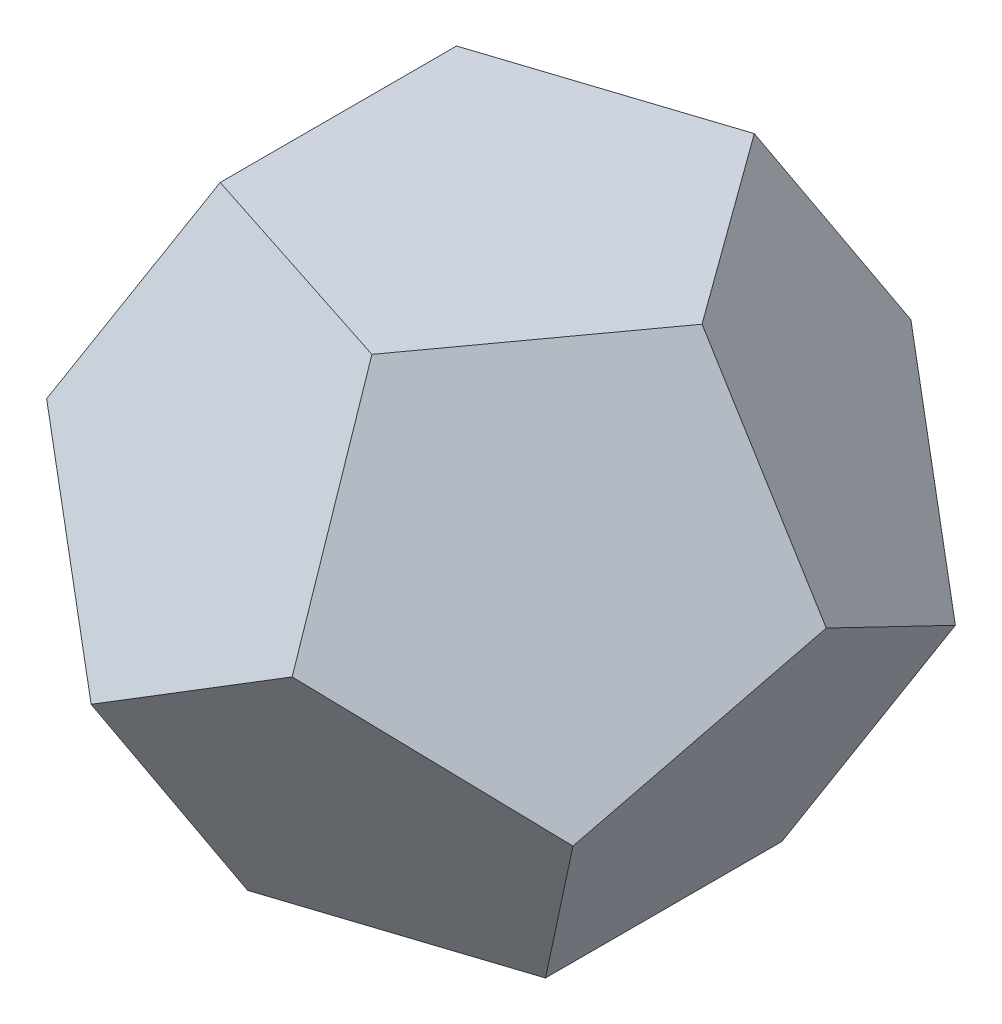
SolidWorks part; units mm, degrees
ref_plane "Vorderansicht-XY" through (0, 0, 0) normal (0, 0, 1) x (1, 0, 0)
ref_plane "Draufsicht-ZX" through (0, 0, 0) normal (0, 1, 0) x (1, 0, 0)
ref_plane "Seitenansicht-YZ" through (0, 0, 0) normal (1, 0, 0) x (0, 0, -1)
sketch "Skizze1" plane through (0, 0, 0) normal (0, 1, 0) x (1, 0, 0)
  line L0 (-37.8505, 0) -> (37.8505, 0) construction
  line L1 (42.5325, 0) -> (13.1433, 40.4508)
  line L2 (13.1433, 40.4508) -> (-34.4095, 25)
  line L3 (-34.4095, 25) -> (-34.4095, -25)
  line L4 (-34.4095, -25) -> (13.1433, -40.4508)
  line L5 (13.1433, -40.4508) -> (42.5325, 0)
  circle A0 centre (0, 0) radius 34.4095 construction
  dimension "D1" = 50
sketch3d "3D-Skizze1"
  line L0 (13.1433, 0, 40.4508) -> (21.2663, -42.5325, 65.4508)
  line L1 (13.1433, 0, -40.4508) -> (21.2663, -42.5325, -65.4508)
  line L2 (21.2663, -42.5325, -65.4508) -> (-21.2663, -68.8191, -65.4508)
  line L3 (-21.2663, -68.8191, -65.4508) -> (-55.6758, -42.5325, -40.4508)
  line L4 (13.1433, 0, 40.4508) -> (42.5325, 0, 0) construction
  line L5 (-34.4095, 0, 25) -> (-55.6758, -42.5325, 40.4508)
  line L6 (-55.6758, -42.5325, 40.4508) -> (-21.2663, -68.8191, 65.4508)
  line L7 (-21.2663, -68.8191, 65.4508) -> (21.2663, -42.5325, 65.4508)
  line L8 (-34.4095, 0, 25) -> (13.1433, 0, 40.4508) construction
  line L9 (-34.4095, 0, -25) -> (-55.6758, -42.5325, -40.4508)
  line L10 (-55.6758, -42.5325, -40.4508) -> (-68.8191, -68.8191, 0)
  line L11 (-68.8191, -68.8191, 0) -> (-55.6758, -42.5325, 40.4508)
  line L12 (-34.4095, 0, -25) -> (-34.4095, 0, 25) construction
  line L13 (13.1433, 0, -40.4508) -> (-34.4095, 0, -25) construction
  line L14 (-21.2663, -68.8191, -65.4508) -> (-10.6331, 0, -32.7254) construction
  line L15 (21.2663, -42.5325, -65.4508) -> (-45.0427, -21.2663, -32.7254) construction
  line L16 (-21.2663, -68.8191, 65.4508) -> (-10.6331, 0, 32.7254) construction
  line L18 (-55.6758, -42.5325, -40.4508) -> (17.2048, -21.2663, -52.9508) construction
  line L31 (-55.6758, -42.5325, 40.4508) -> (17.2048, -21.2663, 52.9508) construction
  line L32 (21.2663, -42.5325, 65.4508) -> (-45.0427, -21.2663, 32.7254) construction
  line L33 (-55.6758, -42.5325, -40.4508) -> (-45.0427, -21.2663, 32.7254) construction
  line L34 (-68.8191, -68.8191, 0) -> (-34.4095, 0, 0) construction
  line L35 (-55.6758, -42.5325, 40.4508) -> (-45.0427, -21.2663, -32.7254) construction
  point P5 (-15.3884, -30.7768, -47.3607)
  point P41 (-49.798, -30.7768, 0)
  point P43 (-15.3884, -30.7768, 47.3607)
sketch3d "3D-Skizze2"
  line L0 (42.5325, 0, 0) -> (68.8191, -42.5325, 0)
  line L1 (68.8191, -42.5325, 0) -> (55.6758, -68.8191, 40.4508)
  line L2 (55.6758, -68.8191, 40.4508) -> (21.2663, -42.5325, 65.4508)
  line L3 (13.1433, 0, 40.4508) -> (42.5325, 0, 0) construction
  line L4 (55.6758, -68.8191, 40.4508) -> (27.8379, 0, 20.2254) construction
  line L5 (21.2663, -42.5325, 65.4508) -> (55.6758, -21.2663, 0) construction
  line L6 (68.8191, -42.5325, 0) -> (17.2048, -21.2663, 52.9508) construction
  line L7 (68.8191, -42.5325, 0) -> (55.6758, -68.8191, -40.4508)
  line L8 (55.6758, -68.8191, -40.4508) -> (21.2663, -42.5325, -65.4508)
  line L9 (42.5325, 0, 0) -> (13.1433, 0, -40.4508) construction
  line L10 (55.6758, -68.8191, -40.4508) -> (27.8379, 0, -20.2254) construction
  line L11 (68.8191, -42.5325, 0) -> (17.2048, -21.2663, -52.9508) construction
  line L12 (21.2663, -42.5325, -65.4508) -> (55.6758, -21.2663, 0) construction
  line L13 (55.6758, -68.8191, 40.4508) -> (34.4095, -111.3516, 25)
  line L14 (34.4095, -111.3516, 25) -> (34.4095, -111.3516, -25)
  line L15 (34.4095, -111.3516, -25) -> (55.6758, -68.8191, -40.4508)
  line L16 (68.8191, -42.5325, 0) -> (34.4095, -111.3516, 0) construction
  line L17 (55.6758, -68.8191, 40.4508) -> (45.0427, -90.0854, -32.7254) construction
  line L18 (55.6758, -68.8191, -40.4508) -> (45.0427, -90.0854, 32.7254) construction
  line L19 (-21.2663, -68.8191, -65.4508) -> (-13.1433, -111.3516, -40.4508)
  line L20 (-13.1433, -111.3516, -40.4508) -> (34.4095, -111.3516, -25)
  line L21 (55.6758, -68.8191, -40.4508) -> (-17.2048, -90.0854, -52.9508) construction
  line L22 (21.2663, -42.5325, -65.4508) -> (10.6331, -111.3516, -32.7254) construction
  line L23 (-21.2663, -68.8191, -65.4508) -> (45.0427, -90.0854, -32.7254) construction
  line L24 (-21.2663, -68.8191, 65.4508) -> (-13.1433, -111.3516, 40.4508)
  line L25 (-13.1433, -111.3516, 40.4508) -> (34.4095, -111.3516, 25)
  line L26 (-13.1433, -111.3516, 40.4508) -> (38.471, -55.6758, 52.9508) construction
  line L27 (-21.2663, -68.8191, 65.4508) -> (45.0427, -90.0854, 32.7254) construction
  line L28 (-68.8191, -68.8191, 0) -> (-42.5325, -111.3516, 0)
  line L29 (-42.5325, -111.3516, 0) -> (-13.1433, -111.3516, 40.4508)
  line L30 (-34.4095, 0, 25) -> (13.1433, 0, 40.4508) construction
  line L31 (-55.6758, -42.5325, 40.4508) -> (-27.8379, -111.3516, 20.2254) construction
  line L32 (-68.8191, -68.8191, 0) -> (-17.2048, -90.0854, 52.9508) construction
  line L33 (-13.1433, -111.3516, -40.4508) -> (-42.5325, -111.3516, 0)
  point P10 (40.2874, -30.7768, 29.2705)
  point P21 (40.2874, -30.7768, -29.2705)
  point P25 (49.798, -80.5748, 0)
  point P33 (15.3884, -80.5748, -47.3607)
  point P34 (15.3884, -80.5748, 47.3607)
  point P48 (-40.2874, -80.5748, 29.2705)
surface "Oberfläche-Ebene1" sketch "Skizze1"
ref_plane "Ebene2" through (22.2703, 13.7638, -16.1803) normal (-0.7236, -0.4472, 0.5257) x (0.4472, 0.2764, 0.8507)
sketch "Skizze2" plane through (22.2703, 13.7638, -16.1803) normal (-0.7236, -0.4472, 0.5257) x (0.4472, 0.2764, 0.8507)
  line L0 (19.0211, -22.3607) -> (-28.5317, -6.9098) construction
  line L1 (19.0211, -22.3607) -> (-28.5317, -6.9098)
  line L2 (19.0211, -22.3607) -> (19.0211, -72.3607) construction
  line L3 (19.0211, -22.3607) -> (19.0211, -72.3607)
  line L4 (19.0211, -72.3607) -> (-28.5317, -87.8115) construction
  line L5 (19.0211, -72.3607) -> (-28.5317, -87.8115)
  line L6 (-28.5317, -87.8115) -> (-57.921, -47.3607) construction
  line L7 (-28.5317, -87.8115) -> (-57.921, -47.3607)
  line L8 (-28.5317, -6.9098) -> (-57.921, -47.3607) construction
  line L9 (-28.5317, -6.9098) -> (-57.921, -47.3607)
surface "Oberfläche-Ebene2" sketch "Skizze2"
ref_plane "Ebene3" through (22.2703, 13.7638, 16.1803) normal (-0.7236, -0.4472, -0.5257) x (-0.4472, -0.2764, 0.8507)
sketch "Skizze3" plane through (22.2703, 13.7638, 16.1803) normal (-0.7236, -0.4472, -0.5257) x (-0.4472, -0.2764, 0.8507)
  line L0 (-19.0211, -22.3607) -> (-19.0211, -72.3607) construction
  line L1 (-19.0211, -72.3607) -> (28.5317, -87.8115) construction
  line L2 (28.5317, -87.8115) -> (57.921, -47.3607) construction
  line L3 (28.5317, -6.9098) -> (57.921, -47.3607) construction
  line L4 (28.5317, -6.9098) -> (-19.0211, -22.3607) construction
  line L5 (-19.0211, -22.3607) -> (-19.0211, -72.3607)
  line L6 (-19.0211, -72.3607) -> (28.5317, -87.8115)
  line L7 (28.5317, -87.8115) -> (57.921, -47.3607)
  line L8 (28.5317, -6.9098) -> (57.921, -47.3607)
  line L9 (28.5317, -6.9098) -> (-19.0211, -22.3607)
surface "Oberfläche-Ebene3" sketch "Skizze3"
ref_plane "Ebene4" through (-8.5065, 13.7638, 26.1803) normal (0.2764, -0.4472, -0.8507) x (-0.961, -0.1286, -0.2446)
sketch "Skizze4" plane through (-8.5065, 13.7638, 26.1803) normal (0.2764, -0.4472, -0.8507) x (-0.961, -0.1286, -0.2446)
  line L0 (13.277, -91.3709) -> (-30.9796, -68.1039) construction
  line L1 (49.0813, -56.4703) -> (13.277, -91.3709) construction
  line L2 (-22.5273, -18.8234) -> (-30.9796, -68.1039) construction
  line L3 (26.953, -11.6335) -> (49.0813, -56.4703) construction
  line L4 (26.953, -11.6335) -> (-22.5273, -18.8234) construction
  line L5 (13.277, -91.3709) -> (-30.9796, -68.1039)
  line L6 (49.0813, -56.4703) -> (13.277, -91.3709)
  line L7 (-22.5273, -18.8234) -> (-30.9796, -68.1039)
  line L8 (26.953, -11.6335) -> (49.0813, -56.4703)
  line L9 (26.953, -11.6335) -> (-22.5273, -18.8234)
surface "Oberfläche-Ebene4" sketch "Skizze4"
ref_plane "Ebene5" through (-27.5276, 13.7638, 0) normal (0.8944, -0.4472, 0) x (0, 0, -1)
sketch "Skizze5" plane through (-27.5276, 13.7638, 0) normal (0.8944, -0.4472, 0) x (0, 0, -1)
  line L0 (40.4508, -62.9412) -> (0, -92.3305) construction
  line L1 (0, -92.3305) -> (-40.4508, -62.9412) construction
  line L2 (-25, -15.3884) -> (-40.4508, -62.9412) construction
  line L3 (25, -15.3884) -> (40.4508, -62.9412) construction
  line L4 (25, -15.3884) -> (-25, -15.3884) construction
  line L5 (40.4508, -62.9412) -> (0, -92.3305)
  line L6 (0, -92.3305) -> (-40.4508, -62.9412)
  line L7 (-25, -15.3884) -> (-40.4508, -62.9412)
  line L8 (25, -15.3884) -> (40.4508, -62.9412)
  line L9 (25, -15.3884) -> (-25, -15.3884)
surface "Oberfläche-Ebene5" sketch "Skizze5"
ref_plane "Ebene6" through (-8.5065, 13.7638, -26.1803) normal (0.2764, -0.4472, 0.8507) x (0.961, 0.1286, -0.2446)
sketch "Skizze6" plane through (-8.5065, 13.7638, -26.1803) normal (0.2764, -0.4472, 0.8507) x (0.961, 0.1286, -0.2446)
  line L0 (-26.953, -11.6335) -> (-49.0813, -56.4703) construction
  line L1 (-13.277, -91.3709) -> (-49.0813, -56.4703) construction
  line L2 (30.9796, -68.1039) -> (-13.277, -91.3709) construction
  line L3 (22.5273, -18.8234) -> (30.9796, -68.1039) construction
  line L4 (22.5273, -18.8234) -> (-26.953, -11.6335) construction
  line L5 (-26.953, -11.6335) -> (-49.0813, -56.4703)
  line L6 (-13.277, -91.3709) -> (-49.0813, -56.4703)
  line L7 (30.9796, -68.1039) -> (-13.277, -91.3709)
  line L8 (22.5273, -18.8234) -> (30.9796, -68.1039)
  line L9 (22.5273, -18.8234) -> (-26.953, -11.6335)
surface "Oberfläche-Ebene6" sketch "Skizze6"
ref_plane "Ebene7" through (22.2703, -36.0341, 68.541) normal (-0.2764, 0.4472, -0.8507) x (-0.961, -0.1286, 0.2446)
sketch "Skizze7" plane through (22.2703, -36.0341, 68.541) normal (-0.2764, 0.4472, -0.8507) x (-0.961, -0.1286, 0.2446)
  line L0 (45.3013, -30.457) -> (36.8491, -79.7374) construction
  line L1 (36.8491, -79.7374) -> (-12.6313, -86.9273) construction
  line L2 (-34.7596, -42.0905) -> (-12.6313, -86.9273) construction
  line L3 (-34.7596, -42.0905) -> (1.0448, -7.1899) construction
  line L4 (45.3013, -30.457) -> (1.0448, -7.1899) construction
  line L5 (45.3013, -30.457) -> (36.8491, -79.7374)
  line L6 (36.8491, -79.7374) -> (-12.6313, -86.9273)
  line L7 (-34.7596, -42.0905) -> (-12.6313, -86.9273)
  line L8 (-34.7596, -42.0905) -> (1.0448, -7.1899)
  line L9 (45.3013, -30.457) -> (1.0448, -7.1899)
surface "Oberfläche-Ebene7" sketch "Skizze7"
ref_plane "Ebene8" through (-58.3045, -36.0341, 42.3607) normal (0.7236, 0.4472, -0.5257) x (-0.4472, -0.2764, -0.8507)
sketch "Skizze8" plane through (-58.3045, -36.0341, 42.3607) normal (0.7236, 0.4472, -0.5257) x (-0.4472, -0.2764, -0.8507)
  line L0 (49.798, -22.3607) -> (49.798, -72.3607) construction
  line L1 (49.798, -22.3607) -> (2.2451, -6.9098) construction
  line L2 (2.2451, -6.9098) -> (-27.1441, -47.3607) construction
  line L3 (-27.1441, -47.3607) -> (2.2451, -87.8115) construction
  line L4 (49.798, -72.3607) -> (2.2451, -87.8115) construction
  line L5 (49.798, -72.3607) -> (2.2451, -87.8115)
  line L6 (-27.1441, -47.3607) -> (2.2451, -87.8115)
  line L7 (2.2451, -6.9098) -> (-27.1441, -47.3607)
  line L8 (49.798, -22.3607) -> (2.2451, -6.9098)
  line L9 (49.798, -22.3607) -> (49.798, -72.3607)
surface "Oberfläche-Ebene8" sketch "Skizze8"
ref_plane "Ebene9" through (-58.3045, -36.0341, -42.3607) normal (0.7236, 0.4472, 0.5257) x (0.4472, 0.2764, -0.8507)
sketch "Skizze9" plane through (-58.3045, -36.0341, -42.3607) normal (0.7236, 0.4472, 0.5257) x (0.4472, 0.2764, -0.8507)
  line L0 (27.1441, -47.3607) -> (-2.2451, -87.8115) construction
  line L1 (-2.2451, -87.8115) -> (-49.798, -72.3607) construction
  line L2 (-49.798, -22.3607) -> (-49.798, -72.3607) construction
  line L3 (-2.2451, -6.9098) -> (-49.798, -22.3607) construction
  line L4 (27.1441, -47.3607) -> (-2.2451, -6.9098) construction
  line L5 (27.1441, -47.3607) -> (-2.2451, -87.8115)
  line L6 (-2.2451, -87.8115) -> (-49.798, -72.3607)
  line L7 (-49.798, -22.3607) -> (-49.798, -72.3607)
  line L8 (-2.2451, -6.9098) -> (-49.798, -22.3607)
  line L9 (27.1441, -47.3607) -> (-2.2451, -6.9098)
surface "Oberfläche-Ebene9" sketch "Skizze9"
ref_plane "Ebene10" through (22.2703, -36.0341, -68.541) normal (0.2764, -0.4472, -0.8507) x (-0.961, -0.1286, -0.2446)
sketch "Skizze10" plane through (22.2703, -36.0341, -68.541) normal (0.2764, -0.4472, -0.8507) x (-0.961, -0.1286, -0.2446)
  line L0 (-12.6313, -86.9273) -> (-34.7596, -42.0905) construction
  line L1 (36.8491, -79.7374) -> (-12.6313, -86.9273) construction
  line L2 (45.3013, -30.457) -> (36.8491, -79.7374) construction
  line L3 (1.0448, -7.1899) -> (45.3013, -30.457) construction
  line L4 (-34.7596, -42.0905) -> (1.0448, -7.1899) construction
  line L5 (-12.6313, -86.9273) -> (-34.7596, -42.0905)
  line L6 (36.8491, -79.7374) -> (-12.6313, -86.9273)
  line L7 (45.3013, -30.457) -> (36.8491, -79.7374)
  line L8 (1.0448, -7.1899) -> (45.3013, -30.457)
  line L9 (-34.7596, -42.0905) -> (1.0448, -7.1899)
surface "Oberfläche-Ebene10" sketch "Skizze10"
ref_plane "Ebene11" through (72.0683, -36.0341, 0) normal (0.8944, -0.4472, 0) x (0, 0, -1)
sketch "Skizze11" plane through (72.0683, -36.0341, 0) normal (0.8944, -0.4472, 0) x (0, 0, -1)
  line L0 (-40.4508, -36.6547) -> (-25, -84.2075) construction
  line L1 (-25, -84.2075) -> (25, -84.2075) construction
  line L2 (25, -84.2075) -> (40.4508, -36.6547) construction
  line L3 (0, -7.2654) -> (40.4508, -36.6547) construction
  line L4 (0, -7.2654) -> (-40.4508, -36.6547) construction
  line L5 (-40.4508, -36.6547) -> (-25, -84.2075)
  line L6 (-25, -84.2075) -> (25, -84.2075)
  line L7 (25, -84.2075) -> (40.4508, -36.6547)
  line L8 (0, -7.2654) -> (40.4508, -36.6547)
  line L9 (0, -7.2654) -> (-40.4508, -36.6547)
surface "Oberfläche-Ebene11" sketch "Skizze11"
ref_plane "Ebene12" through (0, -111.3516, 0) normal (0, 1, 0) x (1, 0, 0)
sketch "Skizze12" plane through (0, -111.3516, 0) normal (0, 1, 0) x (1, 0, 0)
  line L0 (-13.1433, -40.4508) -> (34.4095, -25) construction
  line L1 (-42.5325, 0) -> (-13.1433, -40.4508) construction
  line L2 (-13.1433, 40.4508) -> (-42.5325, 0) construction
  line L3 (-13.1433, 40.4508) -> (34.4095, 25) construction
  line L4 (34.4095, -25) -> (34.4095, 25) construction
  line L5 (-13.1433, -40.4508) -> (34.4095, -25)
  line L6 (-42.5325, 0) -> (-13.1433, -40.4508)
  line L7 (-13.1433, 40.4508) -> (-42.5325, 0)
  line L8 (-13.1433, 40.4508) -> (34.4095, 25)
  line L9 (34.4095, -25) -> (34.4095, 25)
surface "Oberfläche-Ebene12" sketch "Skizze12"
surface "Oberfläche-Zusammenfügen1"
sketch3d "3D-Skizze3"
  line L0 (0, 0, 0) -> (40.2874, -30.7768, 29.2705)
  line L1 (40.2874, -30.7768, 29.2705) -> (40.2874, -30.7768, -29.2705)
  line L2 (40.2874, -30.7768, -29.2705) -> (0, 0, 0)
  line L3 (40.2874, -30.7768, 29.2705) -> (-15.3884, -30.7768, 47.3607)
  line L4 (-15.3884, -30.7768, 47.3607) -> (0, 0, 0)
  line L5 (-15.3884, -30.7768, 47.3607) -> (-49.798, -30.7768, 0)
  line L6 (-49.798, -30.7768, 0) -> (0, 0, 0)
  line L7 (-49.798, -30.7768, 0) -> (-15.3884, -30.7768, -47.3607)
  line L8 (-15.3884, -30.7768, -47.3607) -> (0, 0, 0)
  line L9 (-15.3884, -30.7768, -47.3607) -> (40.2874, -30.7768, -29.2705)
  line L10 (-15.3884, -30.7768, -47.3607) -> (15.3884, -80.5748, -47.3607)
  line L11 (15.3884, -80.5748, -47.3607) -> (40.2874, -30.7768, -29.2705)
  line L12 (15.3884, -80.5748, -47.3607) -> (49.798, -80.5748, 0)
  line L13 (49.798, -80.5748, 0) -> (40.2874, -30.7768, -29.2705)
  line L14 (49.798, -80.5748, 0) -> (40.2874, -30.7768, 29.2705)
  line L15 (-49.798, -30.7768, 0) -> (-40.2874, -80.5748, 29.2705)
  line L16 (-40.2874, -80.5748, 29.2705) -> (-15.3884, -30.7768, 47.3607)
  line L17 (-40.2874, -80.5748, 29.2705) -> (15.3884, -80.5748, 47.3607)
  line L18 (15.3884, -80.5748, 47.3607) -> (-15.3884, -30.7768, 47.3607)
  line L19 (15.3884, -80.5748, 47.3607) -> (40.2874, -30.7768, 29.2705)
  line L20 (15.3884, -80.5748, 47.3607) -> (49.798, -80.5748, 0)
  line L21 (-68.8191, -68.8191, 0) -> (-42.5325, -111.3516, 0) construction
  line L22 (-13.1433, -111.3516, -40.4508) -> (-42.5325, -111.3516, 0) construction
  line L23 (-21.2663, -68.8191, -65.4508) -> (-55.6758, -42.5325, -40.4508) construction
  line L24 (-13.1433, -111.3516, 40.4508) -> (34.4095, -111.3516, 25) construction
  line L25 (34.4095, -111.3516, 25) -> (34.4095, -111.3516, -25) construction
  line L26 (-13.1433, -111.3516, -40.4508) -> (34.4095, -111.3516, -25) construction
  line L27 (-49.798, -30.7768, 0) -> (-40.2874, -80.5748, -29.2705)
  line L28 (-40.2874, -80.5748, -29.2705) -> (-40.2874, -80.5748, 29.2705)
  line L29 (15.3884, -80.5748, -47.3607) -> (-40.2874, -80.5748, -29.2705)
  line L30 (-40.2874, -80.5748, -29.2705) -> (-15.3884, -30.7768, -47.3607)
  line L31 (-40.2874, -80.5748, -29.2705) -> (0, -111.3516, 0)
  line L32 (0, -111.3516, 0) -> (15.3884, -80.5748, -47.3607)
  line L33 (-40.2874, -80.5748, 29.2705) -> (0, -111.3516, 0)
  line L34 (15.3884, -80.5748, 47.3607) -> (0, -111.3516, 0)
  line L35 (49.798, -80.5748, 0) -> (0, -111.3516, 0)
  circle A0 centre (-40.2874, -80.5748, -29.2705) radius 34.4095 construction
  circle A1 centre (0, -111.3516, 0) radius 34.4095 construction
  point P22 (-15.3884, -65.1864, -11.1803)
  point P31 (0, -76.9421, 0)
ref_plane "Ebene-y1" through (0, 0, 0) normal (0.1876, 0.7947, 0.5774) x (0.9822, -0.1518, -0.1103)
sketch "Skizze-y1" plane through (0, 0, 0) normal (0.1876, 0.7947, 0.5774) x (0.9822, -0.1518, -0.1103)
  line L0 (41.0156, -41.7705) -> (-15.6665, -56.4058) construction
  line L1 (0, 0) -> (41.0156, -41.7705) construction
  line L2 (-15.6665, -56.4058) -> (0, 0) construction
  line L3 (41.0156, -41.7705) -> (-15.6665, -56.4058)
  line L4 (0, 0) -> (41.0156, -41.7705)
  line L5 (-15.6665, -56.4058) -> (0, 0)
surface "Oberfläche-Ebene-y1" sketch "Skizze-y1"
ref_plane "Ebene-y2" through (0, 0, 0) normal (-0.4911, 0.7947, 0.3568) x (0.8711, 0.448, 0.2012)
sketch "Skizze-y2" plane through (0, 0, 0) normal (-0.4911, 0.7947, 0.3568) x (0.8711, 0.448, 0.2012)
  line L0 (-17.6657, -55.812) -> (0, 0) construction
  line L1 (-57.1674, -12.607) -> (0, 0) construction
  line L2 (-17.6657, -55.812) -> (-57.1674, -12.607) construction
  line L3 (-17.6657, -55.812) -> (0, 0)
  line L4 (-57.1674, -12.607) -> (0, 0)
  line L5 (-17.6657, -55.812) -> (-57.1674, -12.607)
surface "Oberfläche-Ebene-y2" sketch "Skizze-y2"
ref_plane "Ebene-y3" through (0, 0, 0) normal (-0.4911, 0.7947, -0.3568) x (0.8711, 0.448, -0.2012)
sketch "Skizze-y3" plane through (0, 0, 0) normal (-0.4911, 0.7947, -0.3568) x (0.8711, 0.448, -0.2012)
  line L0 (-57.1674, 12.607) -> (0, 0) construction
  line L1 (-57.1674, 12.607) -> (-17.6657, 55.812) construction
  line L2 (-17.6657, 55.812) -> (0, 0) construction
  line L3 (-57.1674, 12.607) -> (0, 0)
  line L4 (-57.1674, 12.607) -> (-17.6657, 55.812)
  line L5 (-17.6657, 55.812) -> (0, 0)
surface "Oberfläche-Ebene-y3" sketch "Skizze-y3"
ref_plane "Ebene-y4" through (0, 0, 0) normal (0.1876, 0.7947, -0.5774) x (0.9822, -0.1518, 0.1103)
sketch "Skizze-y4" plane through (0, 0, 0) normal (0.1876, 0.7947, -0.5774) x (0.9822, -0.1518, 0.1103)
  line L0 (41.0156, 41.7705) -> (0, 0) construction
  line L1 (-15.6665, 56.4058) -> (41.0156, 41.7705) construction
  line L2 (-15.6665, 56.4058) -> (0, 0) construction
  line L3 (41.0156, 41.7705) -> (0, 0)
  line L4 (-15.6665, 56.4058) -> (41.0156, 41.7705)
  line L5 (-15.6665, 56.4058) -> (0, 0)
surface "Oberfläche-Ebene-y4" sketch "Skizze-y4"
ref_plane "Ebene-y5" through (0, 0, 0) normal (0.6071, 0.7947, 0) x (0.7947, -0.6071, 0)
sketch "Skizze-y5" plane through (0, 0, 0) normal (0.6071, 0.7947, 0) x (0.7947, -0.6071, 0)
  line L0 (0, 0) -> (50.698, -29.2705) construction
  line L1 (50.698, -29.2705) -> (50.698, 29.2705) construction
  line L2 (50.698, 29.2705) -> (0, 0) construction
  line L3 (0, 0) -> (50.698, -29.2705)
  line L4 (50.698, -29.2705) -> (50.698, 29.2705)
  line L5 (50.698, 29.2705) -> (0, 0)
surface "Oberfläche-Ebene-y5" sketch "Skizze-y5"
ref_plane "Ebene-y6" through (10.2589, 6.3404, 31.5738) normal (-0.3035, -0.1876, -0.9342) x (-0.9528, 0.0598, 0.2976)
sketch "Skizze-y6" plane through (10.2589, 6.3404, 31.5738) normal (-0.3035, -0.1876, -0.9342) x (-0.9528, 0.0598, 0.2976)
  line L0 (-5.3835, -88.3222) -> (-31.5153, -35.9373) construction
  line L1 (-31.5153, -35.9373) -> (26.9173, -39.4989) construction
  line L2 (-5.3835, -88.3222) -> (26.9173, -39.4989) construction
  line L3 (-5.3835, -88.3222) -> (-31.5153, -35.9373)
  line L4 (-31.5153, -35.9373) -> (26.9173, -39.4989)
  line L5 (-5.3835, -88.3222) -> (26.9173, -39.4989)
surface "Oberfläche-Ebene-y6" sketch "Skizze-y6"
ref_plane "Ebene-y7" through (-16.5993, -10.2589, 51.0875) normal (0.3035, 0.1876, -0.9342) x (-0.9528, 0.0598, -0.2976)
sketch "Skizze-y7" plane through (-16.5993, -10.2589, 51.0875) normal (0.3035, 0.1876, -0.9342) x (-0.9528, 0.0598, -0.2976)
  line L0 (-33.5716, -69.6733) -> (-1.2709, -20.85) construction
  line L1 (24.861, -73.2349) -> (-33.5716, -69.6733) construction
  line L2 (24.861, -73.2349) -> (-1.2709, -20.85) construction
  line L3 (-33.5716, -69.6733) -> (-1.2709, -20.85)
  line L4 (24.861, -73.2349) -> (-33.5716, -69.6733)
  line L5 (24.861, -73.2349) -> (-1.2709, -20.85)
surface "Oberfläche-Ebene-y7" sketch "Skizze-y7"
ref_plane "Ebene-y8" through (-26.8583, 6.3404, 19.5137) normal (-0.7947, 0.1876, 0.5774) x (0.5619, -0.1326, 0.8165)
sketch "Skizze-y8" plane through (-26.8583, 6.3404, 19.5137) normal (-0.7947, 0.1876, 0.5774) x (0.5619, -0.1326, 0.8165)
  line L0 (11.9496, -87.6755) -> (34.1055, -33.4891) construction
  line L1 (34.1055, -33.4891) -> (-23.8993, -41.3948) construction
  line L2 (-23.8993, -41.3948) -> (11.9496, -87.6755) construction
  line L3 (11.9496, -87.6755) -> (34.1055, -33.4891)
  line L4 (34.1055, -33.4891) -> (-23.8993, -41.3948)
  line L5 (-23.8993, -41.3948) -> (11.9496, -87.6755)
surface "Oberfläche-Ebene-y8" sketch "Skizze-y8"
ref_plane "Ebene-y9" through (-53.7165, -10.2589, 0) normal (-0.9822, -0.1876, 0) x (0, 0, 1)
sketch "Skizze-y9" plane through (-53.7165, -10.2589, 0) normal (-0.9822, -0.1876, 0) x (0, 0, 1)
  line L0 (-29.2705, -71.5867) -> (29.2705, -71.5867) construction
  line L1 (0, -20.8887) -> (29.2705, -71.5867) construction
  line L2 (0, -20.8887) -> (-29.2705, -71.5867) construction
  line L3 (-29.2705, -71.5867) -> (29.2705, -71.5867)
  line L4 (0, -20.8887) -> (29.2705, -71.5867)
  line L5 (0, -20.8887) -> (-29.2705, -71.5867)
surface "Oberfläche-Ebene-y9" sketch "Skizze-y9"
ref_plane "Ebene-y10" through (-26.8583, 6.3404, -19.5137) normal (0.7947, -0.1876, 0.5774) x (0.5619, -0.1326, -0.8165)
sketch "Skizze-y10" plane through (-26.8583, 6.3404, -19.5137) normal (0.7947, -0.1876, 0.5774) x (0.5619, -0.1326, -0.8165)
  line L0 (-23.8993, -41.3948) -> (11.9496, -87.6755) construction
  line L1 (-23.8993, -41.3948) -> (34.1055, -33.4891) construction
  line L2 (11.9496, -87.6755) -> (34.1055, -33.4891) construction
  line L3 (-23.8993, -41.3948) -> (11.9496, -87.6755)
  line L4 (-23.8993, -41.3948) -> (34.1055, -33.4891)
  line L5 (11.9496, -87.6755) -> (34.1055, -33.4891)
surface "Oberfläche-Ebene-y10" sketch "Skizze-y10"
ref_plane "Ebene-y11" through (-16.5993, -10.2589, -51.0875) normal (-0.3035, -0.1876, -0.9342) x (-0.9528, 0.0598, 0.2976)
sketch "Skizze-y11" plane through (-16.5993, -10.2589, -51.0875) normal (-0.3035, -0.1876, -0.9342) x (-0.9528, 0.0598, 0.2976)
  line L0 (-33.5716, -69.6733) -> (24.861, -73.2349) construction
  line L1 (24.861, -73.2349) -> (-1.2709, -20.85) construction
  line L2 (-1.2709, -20.85) -> (-33.5716, -69.6733) construction
  line L3 (-33.5716, -69.6733) -> (24.861, -73.2349)
  line L4 (24.861, -73.2349) -> (-1.2709, -20.85)
  line L5 (-1.2709, -20.85) -> (-33.5716, -69.6733)
surface "Oberfläche-Ebene-y11" sketch "Skizze-y11"
ref_plane "Ebene-y12" through (10.2589, 6.3404, -31.5738) normal (-0.3035, -0.1876, 0.9342) x (0.9528, -0.0598, 0.2976)
sketch "Skizze-y12" plane through (10.2589, 6.3404, -31.5738) normal (-0.3035, -0.1876, 0.9342) x (0.9528, -0.0598, 0.2976)
  line L0 (-26.9173, -39.4989) -> (5.3835, -88.3222) construction
  line L1 (-26.9173, -39.4989) -> (31.5153, -35.9373) construction
  line L2 (5.3835, -88.3222) -> (31.5153, -35.9373) construction
  line L3 (-26.9173, -39.4989) -> (5.3835, -88.3222)
  line L4 (-26.9173, -39.4989) -> (31.5153, -35.9373)
  line L5 (5.3835, -88.3222) -> (31.5153, -35.9373)
surface "Oberfläche-Ebene-y12" sketch "Skizze-y12"
ref_plane "Ebene-y13" through (43.4576, -10.2589, -31.5738) normal (0.7947, -0.1876, -0.5774) x (-0.5619, 0.1326, -0.8165)
sketch "Skizze-y13" plane through (43.4576, -10.2589, -31.5738) normal (0.7947, -0.1876, -0.5774) x (-0.5619, 0.1326, -0.8165)
  line L0 (19.3349, -74.8838) -> (-38.6698, -66.9781) construction
  line L1 (19.3349, -74.8838) -> (-2.8209, -20.6974) construction
  line L2 (-38.6698, -66.9781) -> (-2.8209, -20.6974) construction
  line L3 (19.3349, -74.8838) -> (-38.6698, -66.9781)
  line L4 (19.3349, -74.8838) -> (-2.8209, -20.6974)
  line L5 (-38.6698, -66.9781) -> (-2.8209, -20.6974)
surface "Oberfläche-Ebene-y13" sketch "Skizze-y13"
ref_plane "Ebene-y14" through (33.1986, 6.3404, 0) normal (-0.9822, -0.1876, 0) x (0, 0, 1)
sketch "Skizze-y14" plane through (33.1986, 6.3404, 0) normal (-0.9822, -0.1876, 0) x (0, 0, 1)
  line L0 (0, -88.4861) -> (-29.2705, -37.7881) construction
  line L1 (29.2705, -37.7881) -> (-29.2705, -37.7881) construction
  line L2 (0, -88.4861) -> (29.2705, -37.7881) construction
  line L3 (0, -88.4861) -> (-29.2705, -37.7881)
  line L4 (29.2705, -37.7881) -> (-29.2705, -37.7881)
  line L5 (0, -88.4861) -> (29.2705, -37.7881)
surface "Oberfläche-Ebene-y14" sketch "Skizze-y14"
ref_plane "Ebene-y15" through (43.4576, -10.2589, 31.5738) normal (-0.7947, 0.1876, -0.5774) x (-0.5619, 0.1326, 0.8165)
sketch "Skizze-y15" plane through (43.4576, -10.2589, 31.5738) normal (-0.7947, 0.1876, -0.5774) x (-0.5619, 0.1326, 0.8165)
  line L0 (-38.6698, -66.9781) -> (-2.8209, -20.6974) construction
  line L1 (19.3349, -74.8838) -> (-38.6698, -66.9781) construction
  line L2 (19.3349, -74.8838) -> (-2.8209, -20.6974) construction
  line L3 (-38.6698, -66.9781) -> (-2.8209, -20.6974)
  line L4 (19.3349, -74.8838) -> (-38.6698, -66.9781)
  line L5 (19.3349, -74.8838) -> (-2.8209, -20.6974)
surface "Oberfläche-Ebene-y15" sketch "Skizze-y15"
ref_plane "Ebene-y16" through (-16.5993, -70.3159, 51.0875) normal (0.1876, 0.7947, -0.5774) x (0.9822, -0.1518, 0.1103)
sketch "Skizze-y16" plane through (-16.5993, -70.3159, 51.0875) normal (0.1876, 0.7947, -0.5774) x (0.9822, -0.1518, 0.1103)
  line L0 (32.5659, 9.0451) -> (16.8993, 65.4508) construction
  line L1 (-24.1162, 23.6803) -> (32.5659, 9.0451) construction
  line L2 (-24.1162, 23.6803) -> (16.8993, 65.4508) construction
  line L3 (32.5659, 9.0451) -> (16.8993, 65.4508)
  line L4 (-24.1162, 23.6803) -> (32.5659, 9.0451)
  line L5 (-24.1162, 23.6803) -> (16.8993, 65.4508)
surface "Oberfläche-Ebene-y16" sketch "Skizze-y16"
ref_plane "Ebene-y17" through (-53.7165, -70.3159, 0) normal (0.6071, 0.7947, 0) x (0.7947, -0.6071, 0)
sketch "Skizze-y17" plane through (-53.7165, -70.3159, 0) normal (0.6071, 0.7947, 0) x (0.7947, -0.6071, 0)
  line L0 (16.8993, -29.2705) -> (67.5973, 0) construction
  line L1 (16.8993, 29.2705) -> (67.5973, 0) construction
  line L2 (16.8993, 29.2705) -> (16.8993, -29.2705) construction
  line L3 (16.8993, -29.2705) -> (67.5973, 0)
  line L4 (16.8993, 29.2705) -> (67.5973, 0)
  line L5 (16.8993, 29.2705) -> (16.8993, -29.2705)
surface "Oberfläche-Ebene-y17" sketch "Skizze-y17"
ref_plane "Ebene-y18" through (-16.5993, -70.3159, -51.0875) normal (-0.1876, -0.7947, -0.5774) x (-0.9822, 0.1518, 0.1103)
sketch "Skizze-y18" plane through (-16.5993, -70.3159, -51.0875) normal (-0.1876, -0.7947, -0.5774) x (-0.9822, 0.1518, 0.1103)
  line L0 (24.1162, -23.6803) -> (-16.8993, -65.4508) construction
  line L1 (-16.8993, -65.4508) -> (-32.5659, -9.0451) construction
  line L2 (-32.5659, -9.0451) -> (24.1162, -23.6803) construction
  line L3 (24.1162, -23.6803) -> (-16.8993, -65.4508)
  line L4 (-16.8993, -65.4508) -> (-32.5659, -9.0451)
  line L5 (-32.5659, -9.0451) -> (24.1162, -23.6803)
surface "Oberfläche-Ebene-y18" sketch "Skizze-y18"
ref_plane "Ebene-y19" through (43.4576, -70.3159, -31.5738) normal (0.4911, -0.7947, -0.3568) x (-0.8711, -0.448, -0.2012)
sketch "Skizze-y19" plane through (43.4576, -70.3159, -31.5738) normal (0.4911, -0.7947, -0.3568) x (-0.8711, -0.448, -0.2012)
  line L0 (49.8887, -45.6127) -> (32.223, 10.1993) construction
  line L1 (-7.2787, -33.0056) -> (49.8887, -45.6127) construction
  line L2 (32.223, 10.1993) -> (-7.2787, -33.0056) construction
  line L3 (49.8887, -45.6127) -> (32.223, 10.1993)
  line L4 (-7.2787, -33.0056) -> (49.8887, -45.6127)
  line L5 (32.223, 10.1993) -> (-7.2787, -33.0056)
surface "Oberfläche-Ebene-y19" sketch "Skizze-y19"
ref_plane "Ebene-y20" through (43.4576, -70.3159, 31.5738) normal (-0.4911, 0.7947, -0.3568) x (0.8711, 0.448, -0.2012)
sketch "Skizze-y20" plane through (43.4576, -70.3159, 31.5738) normal (-0.4911, 0.7947, -0.3568) x (0.8711, 0.448, -0.2012)
  line L0 (-32.223, -10.1993) -> (7.2787, 33.0056) construction
  line L1 (7.2787, 33.0056) -> (-49.8887, 45.6127) construction
  line L2 (-32.223, -10.1993) -> (-49.8887, 45.6127) construction
  line L3 (-32.223, -10.1993) -> (7.2787, 33.0056)
  line L4 (7.2787, 33.0056) -> (-49.8887, 45.6127)
  line L5 (-32.223, -10.1993) -> (-49.8887, 45.6127)
surface "Oberfläche-Ebene-y20" sketch "Skizze-y20"
surface "Oberfläche-Zusammenfügen2"
